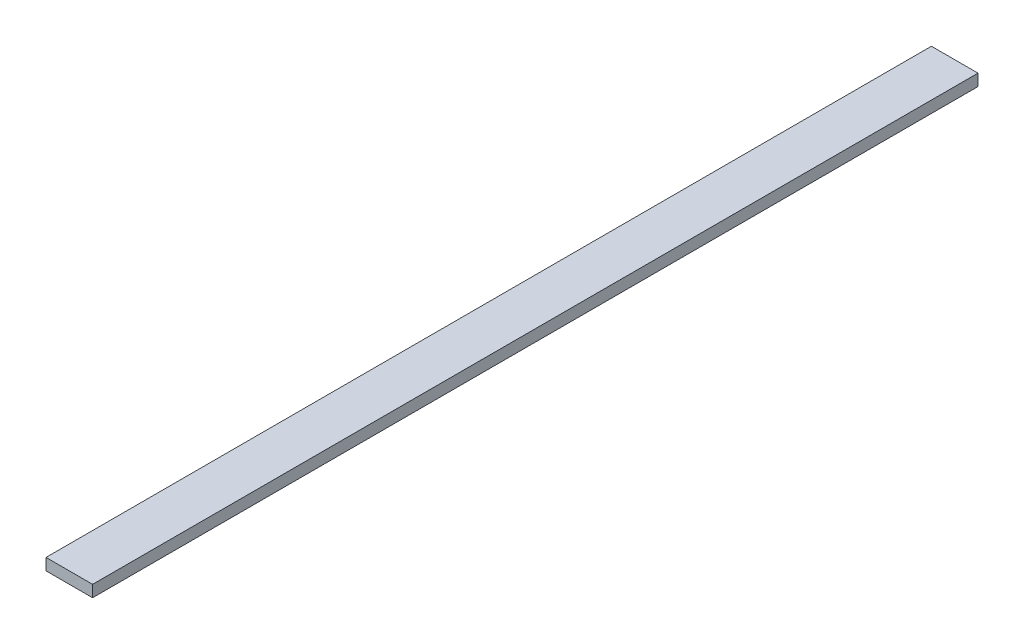
SolidWorks part; units mm, degrees
material "Plywood"
ref_plane "Front Plane" through (0, 0, 0) normal (0, 0, 1) x (1, 0, 0)
ref_plane "Top Plane" through (0, 0, 0) normal (0, 1, 0) x (1, 0, 0)
ref_plane "Right Plane" through (0, 0, 0) normal (1, 0, 0) x (0, 0, -1)
sketch "Sketch1" plane through (0, 0, 0) normal (0, 0, 1) x (1, 0, 0)
  line L1 (0, 0) -> (12.7, 0)
  line L2 (0, 0) -> (0, 3.175)
  line L3 (0, 3.175) -> (12.7, 3.175)
  line L4 (12.7, 0) -> (12.7, 3.175)
  dimension "D1" = 12.7
  dimension "D2" = 3.175
extrude "Boss-Extrude1" add sketch "Sketch1" along normal blind 241.3
move or copy body "Body-Move/Copy1" [suppressed] bodies to move or copy 101 parameters "D1"=0, "D2"=0, "D3"=0
